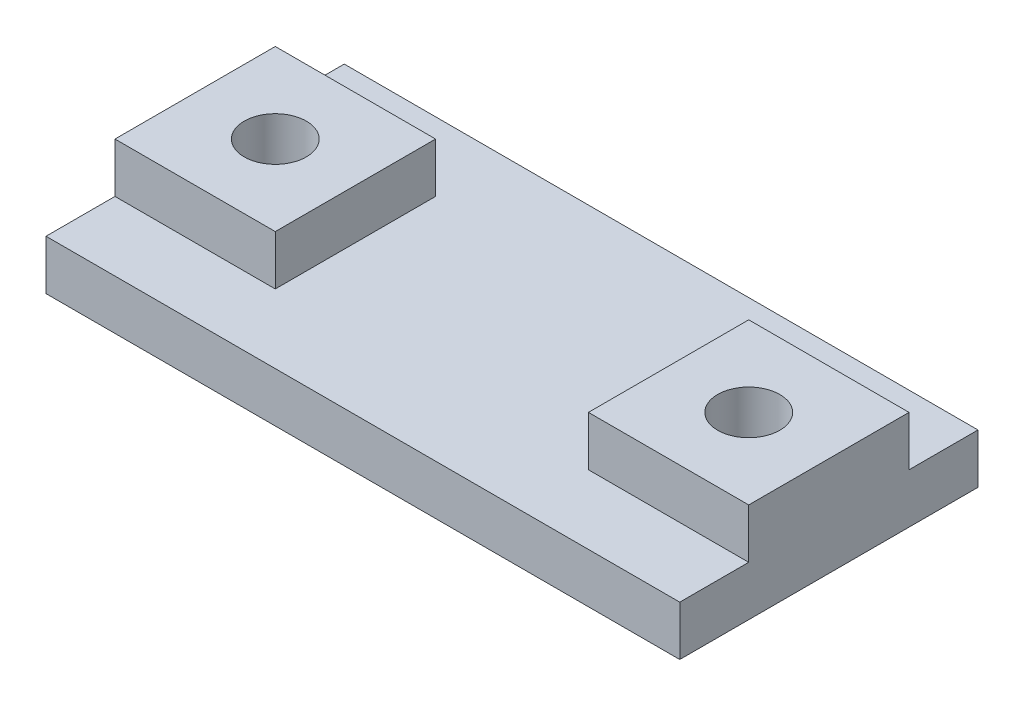
SolidWorks part; units mm, degrees
ref_plane "Front" through (0, 0, 0) normal (0, 0, 1) x (1, 0, 0)
ref_plane "Top" through (0, 0, 0) normal (0, 1, 0) x (1, 0, 0)
ref_plane "Right" through (0, 0, 0) normal (1, 0, 0) x (0, 0, -1)
sketch "Sketch2" plane through (0, 0, 0) normal (0, 1, 0) x (1, 0, 0)
  line L1 (-12.75, -6) -> (12.75, -6)
  line L2 (-12.75, -6) -> (-12.75, 6)
  line L3 (-12.75, 6) -> (12.75, 6)
  line L4 (12.75, -6) -> (12.75, 6)
  line L5 (0, 6) -> (0, -6) construction
  line L6 (-12.75, 0) -> (12.75, 0) construction
  point P0 (0, 0)
  dimension "D1" = 25.5
  dimension "D2" = 12
extrude "Boss-Extrude1" add sketch "Sketch2" along normal blind 2
sketch "Sketch3" plane through (0, 2, 0) normal (0, 1, 0) x (1, 0, 0)
  line L0 (-12.75, 6) -> (-12.75, -6) construction
  line L1 (-12.75, -3.225) -> (-6.3, -3.225)
  line L2 (-12.75, -3.225) -> (-12.75, 3.225)
  line L3 (-12.75, 3.225) -> (-6.3, 3.225)
  line L4 (-6.3, -3.225) -> (-6.3, 3.225)
  line L5 (-9.525, 3.225) -> (-9.525, -3.225) construction
  line L6 (-12.75, 0) -> (-6.3, 0) construction
  line L7 (12.75, -3.225) -> (6.3, -3.225)
  line L8 (12.75, -3.225) -> (12.75, 3.225)
  line L9 (12.75, 3.225) -> (6.3, 3.225)
  line L10 (6.3, -3.225) -> (6.3, 3.225)
  line L11 (9.525, 3.225) -> (9.525, -3.225) construction
  line L12 (12.75, 0) -> (6.3, 0) construction
  line L13 (12.75, -6) -> (12.75, 6) construction
  point P140 (-9.525, 0)
  point P198 (9.525, 0)
  dimension "D1" = 19.05
extrude "Boss-Extrude2" add sketch "Sketch3" along normal blind 2
hole_wizard "M3x0.5 Tapped Hole1" positions "Sketch4" profile "Sketch5" tap size "M3x0.5" standard "ANSI Metric" end condition through all
sketch "Sketch4" plane through (0, 4, 0) normal (0, 1, 0) x (1, 0, 0)
  point P0 (-9.525, 0)
  point P3 (9.525, 0)
sketch "Sketch5" plane through (-9.525, 4, 0) normal (1, 0, 0) x (0, 0, 1)
  line L0 (0, 0) -> (0, 4)
  line L1 (0, 4) -> (1.25, 4)
  line L2 (1.25, 4) -> (1.25, 0)
  line L5 (1.25, 0) -> (0, 0)
  line L11 (0, -6.35) -> (0, 107.95) construction
  dimension "Thru Tap Drill Dia." = 2.5
  dimension "Thru Tap Drill Depth" = 4
cosmetic thread "Hole Thread1" parameters "D2"=3
cosmetic thread "Hole Thread2" parameters "D2"=3
